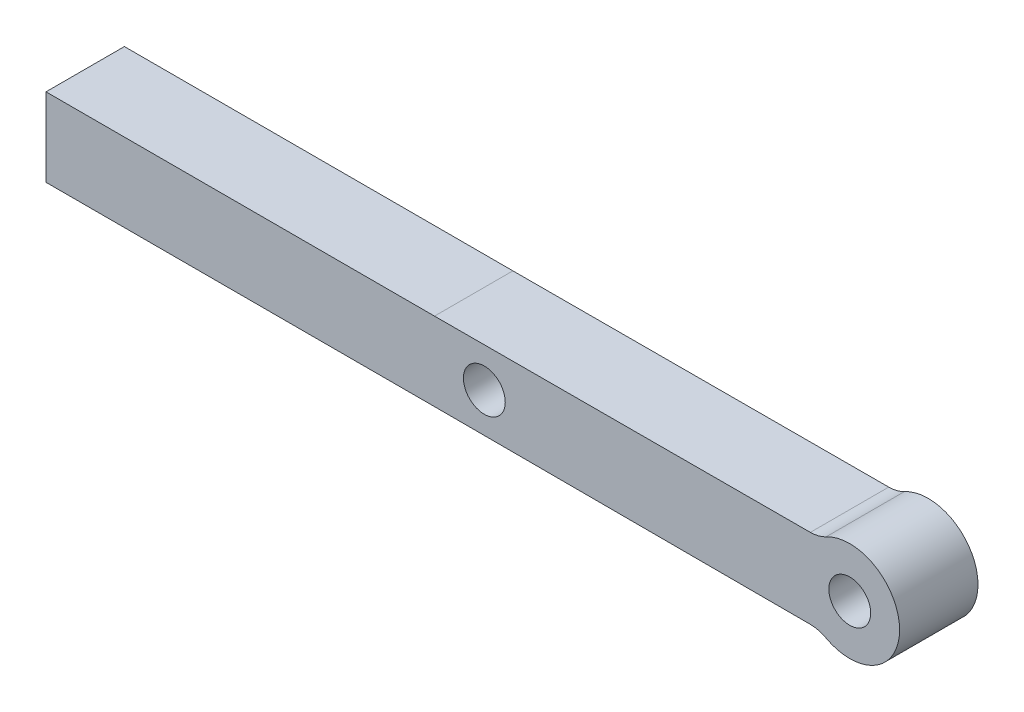
SolidWorks part; units mm, degrees
ref_plane "Front Plane" through (0, 0, 0) normal (0, 0, 1) x (1, 0, 0)
ref_plane "Top Plane" through (0, 0, 0) normal (0, 1, 0) x (1, 0, 0)
ref_plane "Right Plane" through (0, 0, 0) normal (1, 0, 0) x (0, 0, -1)
sketch "Sketch1" plane through (0, 0, 0) normal (0, 0, 1) x (1, 0, 0)
  line L0 (-31.75, 2.9972) -> (-37.7444, 2.9972)
  line L1 (-37.7444, 2.9972) -> (-42.4037, 2.9972)
  line L2 (-31.75, 2.9972) -> (-3.014, 3.0467)
  line L3 (-61.4537, 2.9972) -> (-61.4537, -2.9972)
  line L4 (-31.75, -2.9972) -> (-3.014, -3.0467)
  line L5 (-42.4037, 2.9972) -> (-61.4537, 2.9972)
  line L6 (-37.7444, -2.9972) -> (-31.75, -2.9972)
  line L7 (-42.4037, -2.9972) -> (-37.7444, -2.9972)
  line L8 (-61.4537, -2.9972) -> (-55.1037, -2.9972)
  line L9 (-55.1037, -2.9972) -> (-42.4037, -2.9972)
  circle A0 centre (0, 0) radius 1.6
  arc A1 (-1.811, -3.352) -> (-1.811, 3.352) centre (0, 0) ccw
  arc A2 (-1.811, 3.352) -> (-3.014, 3.0467) centre (-3.0184, 5.5867) cw
  arc A3 (-1.811, -3.352) -> (-3.014, -3.0467) centre (-3.0184, -5.5867) ccw
  circle A4 centre (-27.94, 0) radius 1.6
  point P17 (-31.75, 0)
  dimension "D1" = 2.54
  dimension "D2" = 2.54
  dimension "D3" = 4.6593
extrude "Boss-Extrude1" add sketch "Sketch1" along normal blind 5.9944 contours L2 A2 A1 A3 L4
